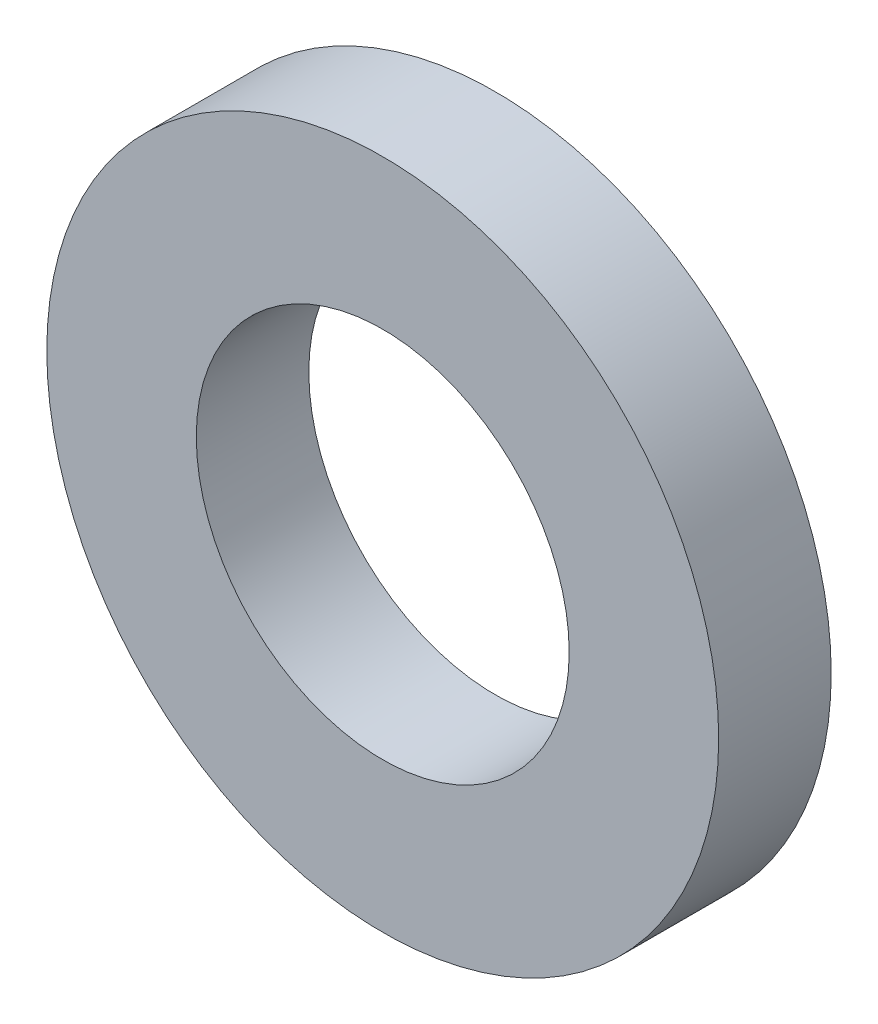
SolidWorks part; units mm, degrees
ref_plane "Front Plane" through (0, 0, 0) normal (0, 0, 1) x (1, 0, 0)
ref_plane "Top Plane" through (0, 0, 0) normal (0, 1, 0) x (1, 0, 0)
ref_plane "Right Plane" through (0, 0, 0) normal (1, 0, 0) x (0, 0, -1)
sketch "Sketch1" plane through (0, 0, 0) normal (0, 0, 1) x (1, 0, 0)
  circle A0 centre (0, 0) radius 1.4732
  circle A1 centre (0, 0) radius 2.6543
extrude "Extrude1" add sketch "Sketch1" along normal blind 0.889
